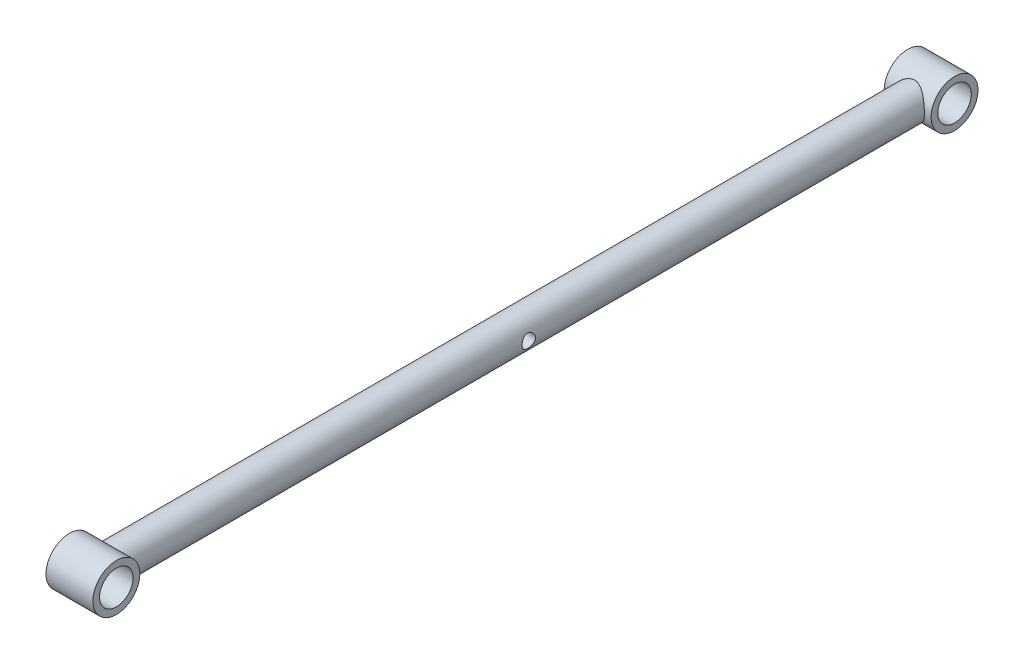
SolidWorks part; units mm, degrees
ref_plane "Front Plane" through (0, 0, 0) normal (0, 0, 1) x (1, 0, 0)
ref_plane "Top Plane" through (0, 0, 0) normal (0, 1, 0) x (1, 0, 0)
ref_plane "Right Plane" through (0, 0, 0) normal (1, 0, 0) x (0, 0, -1)
sketch "Sketch1" plane through (0, 0, 0) normal (0, 0, 1) x (1, 0, 0)
  circle A0 centre (0, 0) radius 12.5
  dimension "D1" = 25
extrude "Boss-Extrude4" add sketch "Sketch1" along normal blind 625.3
sketch "Sketch4" plane through (0, 0, 0) normal (1, 0, 0) x (0, 0, -1)
  line L0 (-625.3, 0) -> (0, 0) construction
  line L1 (-625.3, 12.5) -> (-625.3, -12.5) construction
  line L2 (-312.65, 22.5945) -> (-312.65, -32.9224) construction
  circle A0 centre (-312.65, 0) radius 5
  dimension "D1" = 10
extrude "Cut-Extrude2" cut sketch "Sketch4" against normal mid plane 625.3
sketch "Sketch5" plane through (0, 0, 0) normal (1, 0, 0) x (0, 0, -1)
  line L0 (-312.65, 12.5) -> (-312.65, -28.1799) construction
  line L1 (0, 12.5) -> (-625.3, 12.5) construction
  circle A0 centre (0, 0) radius 12.5
  circle A1 centre (0, 0) radius 17.5
  circle A2 centre (-625.3, 0) radius 12.5
  circle A3 centre (-625.3, 0) radius 17.5
  dimension "D1" = 35
  dimension "D2" = 25
extrude "Boss-Extrude6" add sketch "Sketch5" along normal mid plane 35
sketch "Sketch7" plane through (0, 0, 0) normal (1, 0, 0) x (0, 0, -1)
  line L0 (-625.3, 12.5) -> (-625.3, -12.5) construction
  circle A0 centre (0, 0) radius 12.5
  circle A1 centre (-625.3, 0) radius 12.5
extrude "Cut-Extrude4" cut sketch "Sketch7" against normal mid plane 35
